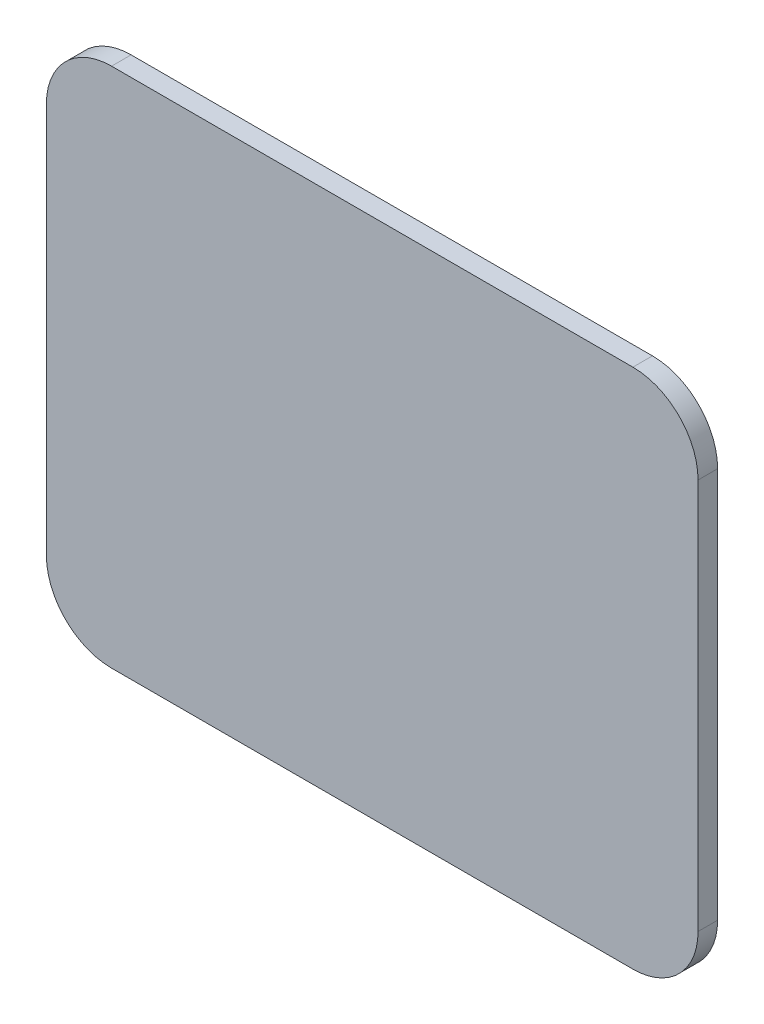
SolidWorks part; units mm, degrees
ref_plane "Płaszczyzna przednia" through (0, 0, 0) normal (0, 0, 1) x (1, 0, 0)
ref_plane "Płaszczyzna górna" through (0, 0, 0) normal (0, 1, 0) x (1, 0, 0)
ref_plane "Płaszczyzna prawa" through (0, 0, 0) normal (1, 0, 0) x (0, 0, -1)
sketch "Szkic1" plane through (0, 0, 0) normal (0, 0, 1) x (1, 0, 0)
  line L1 (10, 0) -> (90, 0)
  line L2 (0, 10) -> (0, 70)
  line L3 (10, 80) -> (90, 80)
  line L4 (100, 10) -> (100, 70)
  arc A0 (90, 80) -> (100, 70) centre (90, 70) cw
  arc A1 (90, 0) -> (100, 10) centre (90, 10) ccw
  arc A2 (10, 0) -> (0, 10) centre (10, 10) cw
  arc A3 (0, 70) -> (10, 80) centre (10, 70) cw
  point P11 (0, 0)
  dimension "D3" = 10
  dimension "D1" = 100
  dimension "D2" = 80
extrude "Dodanie-wyciągnięcie1" add sketch "Szkic1" along normal blind 3
